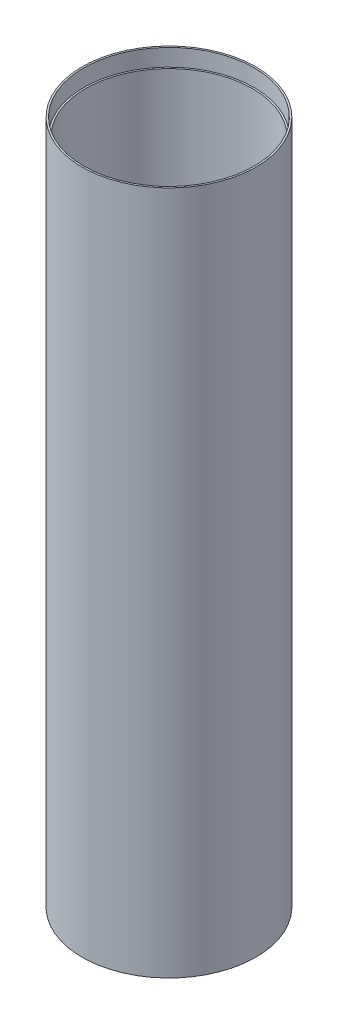
SolidWorks part; units mm, degrees
material "1060 Alloy"
ref_plane "Front Plane" through (0, 0, 0) normal (0, 0, 1) x (1, 0, 0)
ref_plane "Top Plane" through (0, 0, 0) normal (0, 1, 0) x (1, 0, 0)
ref_plane "Right Plane" through (0, 0, 0) normal (1, 0, 0) x (0, 0, -1)
sketch "Sketch1" plane through (0, 0, 0) normal (0, 0, 1) x (1, 0, 0)
  line L0 (0, 0) -> (0, 1000) construction
  line L1 (127, 1000) -> (127, 0)
  line L2 (122, 975) -> (122, 25)
  line L3 (124.5, 1000) -> (127, 1000)
  line L4 (124.5, 0) -> (127, 0)
  line L5 (122, 1000) -> (122, 0) construction
  line L8 (122, 975) -> (124.5, 975)
  line L9 (124.5, 1000) -> (124.5, 975)
  line L11 (122, 25) -> (124.5, 25)
  line L12 (124.5, 0) -> (124.5, 25)
  dimension "D1" = 1000
  dimension "D2" = 1000
  dimension "D3" = 127
  dimension "D5" = 25
  dimension "D6" = 2.5
  dimension "D7" = 2.5
  dimension "D8" = 25
  dimension "D4" = 5
revolve "Revolve1" add sketch "Sketch1" angle 360 about L0
